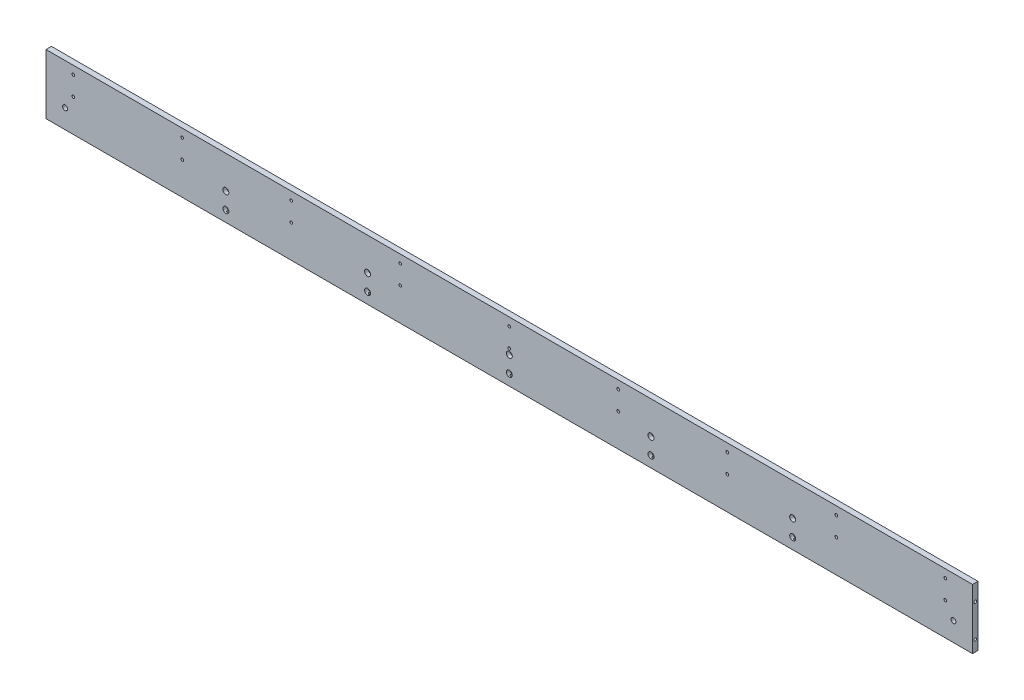
SolidWorks part; units mm, degrees
material "A3钢"
ref_plane "前视基准面" through (0, 0, 0) normal (0, 0, 1) x (1, 0, 0)
ref_plane "上视基准面" through (0, 0, 0) normal (0, 1, 0) x (1, 0, 0)
ref_plane "右视基准面" through (0, 0, 0) normal (1, 0, 0) x (0, 0, -1)
sketch "草图1" plane through (0, 0, 0) normal (0, 0, 1) x (1, 0, 0)
  line L1 (-850, -50) -> (850, -50)
  line L2 (-850, -50) -> (-850, 50)
  line L3 (-850, 50) -> (850, 50)
  line L4 (850, -50) -> (850, 50)
  line L5 (-850, -50) -> (850, 50) construction
  line L6 (-850, 50) -> (850, -50) construction
  point P0 (0, 0)
  dimension "D1" = 1700
  dimension "D2" = 100
extrude "凸台-拉伸1" add sketch "草图1" along normal mid plane 10
sketch "草图2" plane through (0, 0, 5) normal (0, 0, 1) x (1, 0, 0)
  line L0 (0, 619.8775) -> (0, -680.849) construction
  line L1 (-850, 50) -> (-850, -50) construction
  line L2 (-842.5, -90) -> (842.5, -90)
  line L3 (-842.5, -90) -> (-842.5, 90)
  line L4 (-842.5, 90) -> (842.5, 90)
  line L5 (842.5, -90) -> (842.5, 90)
  line L6 (-842.5, -90) -> (842.5, 90) construction
  line L7 (-842.5, 90) -> (842.5, -90) construction
  line L8 (-842.5, 0) -> (1266.3795, 0) construction
  point P3 (0, 0)
  dimension "D1" = 7.5
  dimension "D2" = 180
sketch "草图3" plane through (-850, 0, 0) normal (-1, 0, 0) x (0, 0, 1)
  line L0 (5, -50) -> (-5, -50) construction
  line L1 (0, 30) -> (0, -30) construction
  dimension "D1" = 60
  dimension "D2" = 20
hole_wizard "M6 螺纹孔1" positions "3D草图1" profile "草图5" tap size "M6" standard "GB"
sketch3d "3D草图1"
  point P0 (-850, 30, 0)
  point P3 (-850, -30, 0)
sketch "草图5" plane through (-850, 30, 0) normal (0, 1, 0) x (0, 0, 1)
  line L0 (0, 0) -> (0, 16.5022)
  line L1 (0, 16.5022) -> (2.5, 15)
  line L2 (2.5, 15) -> (2.5, 0)
  line L5 (2.5, 0) -> (0, 0)
  line L10 (0, 16.5022) -> (-2.5, 15) construction
  line L11 (0, -6.35) -> (0, 107.95) construction
  dimension "螺纹孔钻头直径" = 5
  dimension "螺纹孔钻头深度" = 15
  dimension "导头角度" = 118
cosmetic thread "孔螺蚊线2" parameters "D1"=12, "D2"=6
cosmetic thread "孔螺蚊线3" parameters "D1"=12, "D2"=6
sketch "草图6" plane through (0, 0, 5) normal (0, 0, 1) x (1, 0, 0)
  line L0 (800, -10) -> (850, -10) construction
  line L1 (850, -50) -> (850, 50) construction
  line L2 (850, 50) -> (-850, 50) construction
  dimension "D1" = 60
  dimension "D2" = 50
sketch "草图9" plane through (0, 0, -5) normal (0, 0, -1) x (-1, 0, 0)
  line L0 (-951.5279, 0) -> (876.388, 0) construction
  line L1 (-690, 47) -> (-690, -49) construction
  line L2 (-850, -50) -> (-850, 50) construction
  line L3 (0, 268.067) -> (0, -611.0479) construction
  line L4 (690, 47) -> (690, -49) construction
  dimension "D1" = 96
  dimension "D2" = 49
  dimension "D3" = 160
sketch "草图14" plane through (0, 0, 5) normal (0, 0, 1) x (1, 0, 0)
  line L0 (-850, 50) -> (-850, -50) construction
  line L1 (-850, -50) -> (850, -50) construction
  circle A0 centre (-800, -20) radius 4
  dimension "D1" = 50
  dimension "D2" = 30
  dimension "D3" = 8
mirror "镜向1" about plane through (0, 0, 0) normal (1, 0, 0) of "M6 螺纹孔1"
sketch "草图15" plane through (0, -50, 0) normal (0, -1, 0) x (1, 0, 0)
  line L0 (0, 5) -> (0, -33.8431) construction
  line L1 (-850, 5) -> (850, 5) construction
  line L2 (0, 0) -> (-260, 0) construction
  line L3 (-260, 0) -> (-520, 0) construction
  line L4 (-520, 0) -> (-780, 0) construction
  line L5 (-780, 0) -> (-1040, 0) construction
  line L6 (-850, -5) -> (850, -5) construction
  line L7 (0, 0) -> (260, 0) construction
  line L8 (260, 0) -> (520, 0) construction
  line L9 (520, 0) -> (780, 0) construction
  line L10 (780, 0) -> (1040, 0) construction
  dimension "D1" = 260
hole_wizard "M6 螺纹孔2" positions "3D草图2" profile "草图16" tap size "M6" standard "GB"
sketch3d "3D草图2"
  point P6 (-520, -50, 0)
  point P9 (-260, -50, 0)
  point P12 (0, -50, 0)
  point P15 (260, -50, 0)
  point P18 (520, -50, 0)
sketch "草图16" plane through (-520, -50, 0) normal (1, 0, 0) x (0, 0, -1)
  line L0 (0, 0) -> (0, 16.5022)
  line L1 (0, 16.5022) -> (2.5, 15)
  line L2 (2.5, 15) -> (2.5, 0)
  line L5 (2.5, 0) -> (0, 0)
  line L10 (0, 16.5022) -> (-2.5, 15) construction
  line L11 (0, -6.35) -> (0, 107.95) construction
  dimension "螺纹孔钻头直径" = 5
  dimension "螺纹孔钻头深度" = 15
  dimension "导头角度" = 118
cosmetic thread "孔螺蚊线15" parameters "D1"=12, "D2"=6
cosmetic thread "孔螺蚊线16" parameters "D1"=12, "D2"=6
cosmetic thread "孔螺蚊线17" parameters "D1"=12, "D2"=6
cosmetic thread "孔螺蚊线18" parameters "D1"=12, "D2"=6
cosmetic thread "孔螺蚊线19" parameters "D1"=12, "D2"=6
sketch "草图17" plane through (0, 0, 5) normal (0, 0, 1) x (1, 0, 0)
  line L0 (0, 50) -> (0, -437.643) construction
  line L1 (850, 50) -> (-850, 50) construction
  line L2 (0, -30) -> (260, -30) construction
  line L3 (260, -30) -> (520, -30) construction
  line L4 (520, -30) -> (780, -30) construction
  line L5 (-850, -50) -> (850, -50) construction
  line L6 (0, -30) -> (-260, -30) construction
  line L7 (-260, -30) -> (-520, -30) construction
  line L8 (-520, -30) -> (-780, -30) construction
  dimension "D1" = 20
  dimension "D2" = 260
hole_wizard "打孔尺寸(%根据)内六角圆柱头螺钉的类型2" positions "3D草图4" profile "草图19" counterbore size "M6" standard "GB" end condition through all
sketch3d "3D草图4"
  point P3 (520, -30, 5)
  point P6 (260, -30, 5)
  point P9 (0, -30, 5)
  point P12 (-260, -30, 5)
  point P15 (-520, -30, 5)
sketch "草图19" plane through (520, -30, 5) normal (1, 0, 0) x (0, -1, 0)
  line L0 (0, 0) -> (0, 10)
  line L1 (0, 10) -> (3.3, 10)
  line L3 (3.3, 10) -> (3.3, 6.8)
  line L4 (3.3, 6.8) -> (5.5, 6.8)
  line L5 (5.5, 6.8) -> (5.5, 0)
  line L7 (5.5, 0) -> (0, 0)
  line L11 (0, -6.35) -> (0, 107.95) construction
  dimension "通孔孔直径" = 6.6
  dimension "通孔孔深度" = 10
  dimension "柱形沉头孔直径" = 11
  dimension "柱形沉头孔深度" = 6.8
pattern_linear "阵列(线性)1" count 2 spacing 30 along (0, 1, 0) of "打孔尺寸(%根据)内六角圆柱头螺钉的类型2"
sketch "草图20" plane through (0, 0, 5) normal (0, 0, 1) x (1, 0, 0)
  line L0 (0, 226.9088) -> (0, -356.8458) construction
  line L1 (-800, 27.5) -> (-740, 27.5) construction
  line L2 (-850, 50) -> (-850, -50) construction
  line L3 (850, 50) -> (-850, 50) construction
  line L4 (-800, 45) -> (-800, 10) construction
  dimension "D1" = 50
  dimension "D2" = 60
  dimension "D3" = 22.5
  dimension "D4" = 35
hole_wizard "M6 螺纹孔3" positions "3D草图5" profile "草图21" tap size "M6" standard "GB" end condition through all
sketch3d "3D草图5"
  point P0 (-800, 45, 5)
  point P3 (-800, 10, 5)
sketch "草图21" plane through (-800, 45, 5) normal (1, 0, 0) x (0, -1, 0)
  line L0 (0, 0) -> (0, 10)
  line L1 (0, 10) -> (2.5, 10)
  line L2 (2.5, 10) -> (2.5, 0)
  line L5 (2.5, 0) -> (0, 0)
  line L11 (0, -6.35) -> (0, 107.95) construction
  dimension "通孔螺纹孔钻头直径" = 5
  dimension "通孔螺纹孔钻头深度" = 10
cosmetic thread "孔螺蚊线13" parameters "D2"=6
cosmetic thread "孔螺蚊线14" parameters "D2"=6
pattern_linear "阵列(线性)2" count 9 spacing 200 along (1, 0, 0) of "M6 螺纹孔3"
sketch "草图22" plane through (0, 0, 5) normal (0, 0, 1) x (1, 0, 0)
  line L0 (-850, 0) -> (850, 0) construction
  line L1 (-850, 50) -> (-850, -50) construction
  line L2 (850, -50) -> (850, 50) construction
  line L3 (815, 15) -> (815, -15) construction
  line L5 (-850, -50) -> (850, -50) construction
  dimension "D1" = 35
  dimension "D2" = 35
hole_wizard "Ø9.0 (9) 直径孔1" positions "3D草图6" profile "草图24" hole size "Ø9.0" standard "GB" end condition through all
sketch3d "3D草图6"
  point P0 (815, -15, 5)
sketch "草图24" plane through (815, -15, 5) normal (1, 0, 0) x (0, -1, 0)
  line L0 (0, 0) -> (0, 10)
  line L1 (0, 10) -> (4.5, 10)
  line L2 (4.5, 10) -> (4.5, 0)
  line L5 (4.5, 0) -> (0, 0)
  line L11 (0, -6.35) -> (0, 107.95) construction
  dimension "通孔孔直径" = 9
  dimension "通孔孔深度" = 10
mirror "镜向2" about plane through (0, 0, 0) normal (1, 0, 0) of "Ø9.0 (9) 直径孔1"
sketch "草图25" plane through (0, 50, 0) normal (0, 1, 0) x (1, 0, 0)
  line L4 (850, 5) -> (-850, 5)
  line L5 (-850, 5) -> (-850, -5)
  line L6 (-850, -5) -> (850, -5)
  line L7 (850, -5) -> (850, 5)
  line L8 (850, 5) -> (-850, 5)
  line L9 (-850, 5) -> (-850, -5)
  line L10 (-850, -5) -> (850, -5)
  line L11 (850, -5) -> (850, 5)
  dimension "D1" = 0
extrude "凸台-拉伸2" add sketch "草图25" along normal blind 10
